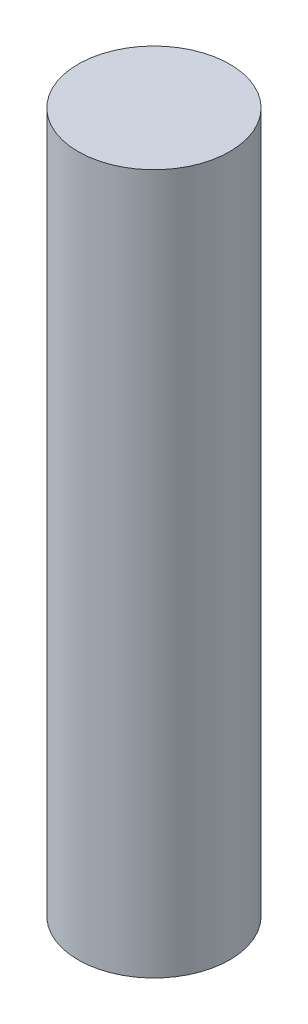
SolidWorks part; units mm, degrees
ref_plane "Front Plane" through (0, 0, 0) normal (0, 0, 1) x (1, 0, 0)
ref_plane "Top Plane" through (0, 0, 0) normal (0, 1, 0) x (1, 0, 0)
ref_plane "Right Plane" through (0, 0, 0) normal (1, 0, 0) x (0, 0, -1)
sketch "Sketch1" plane through (0, 0, 0) normal (0, 1, 0) x (1, 0, 0)
  circle A0 centre (0, 0) radius 2.75
  dimension "D1" = 5.5
extrude "Boss-Extrude1" add sketch "Sketch1" along normal blind 25.4
